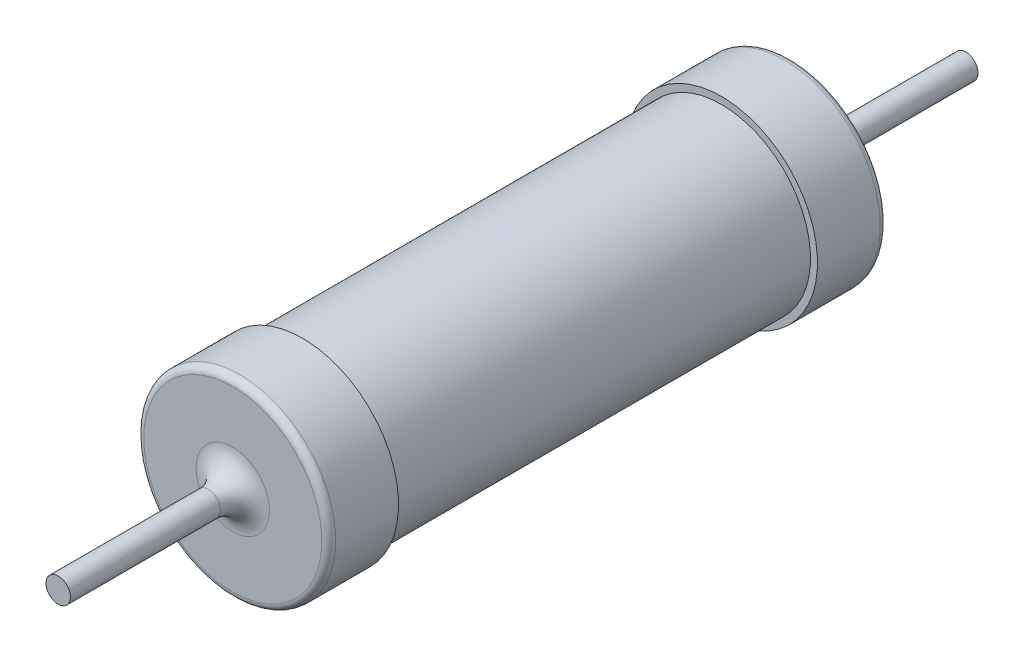
SolidWorks part; units mm, degrees
ref_plane "Front Plane" through (0, 0, 0) normal (0, 0, 1) x (1, 0, 0)
ref_plane "Top Plane" through (0, 0, 0) normal (0, 1, 0) x (1, 0, 0)
ref_plane "Right Plane" through (0, 0, 0) normal (1, 0, 0) x (0, 0, -1)
ref_plane "Plane1" through (0, 0, 8) normal (0, 0, 1) x (1, 0, 0)
sketch "Sketch1" plane through (0, 0, 8) normal (0, 0, 1) x (1, 0, 0)
  circle A0 centre (0, 0) radius 2.75
extrude "Boss-Extrude1" add sketch "Sketch1" against normal blind 2
sketch "Sketch2" plane through (0, 0, 6) normal (0, 0, -1) x (-1, 0, 0)
  circle A0 centre (0, 0) radius 2.55
extrude "Boss-Extrude2" add sketch "Sketch2" along normal blind 12
ref_plane "Plane2" through (0, 0, -6) normal (0, 0, 1) x (1, 0, 0)
sketch "Sketch3" plane through (0, 0, -6) normal (0, 0, 1) x (1, 0, 0)
  circle A0 centre (0, 0) radius 2.75
extrude "Boss-Extrude3" add sketch "Sketch3" against normal blind 2
sketch "Sketch4" plane through (0, 0, 8) normal (0, 0, 1) x (1, 0, 0)
  circle A0 centre (0, 0) radius 0.35
extrude "Boss-Extrude4" add sketch "Sketch4" along normal blind 5
sketch "Sketch5" plane through (0, 0, -8) normal (0, 0, -1) x (-1, 0, 0)
  circle A0 centre (0, 0) radius 0.35
extrude "Boss-Extrude5" add sketch "Sketch5" along normal blind 5
fillet "Fillet1" radius 0.2 2 edges at (-2.75, 0, -8) (-2.75, 0, 8)
fillet "Fillet2" radius 0.7 2 edges at (-0.35, 0, 8) (-0.35, 0, -8)
